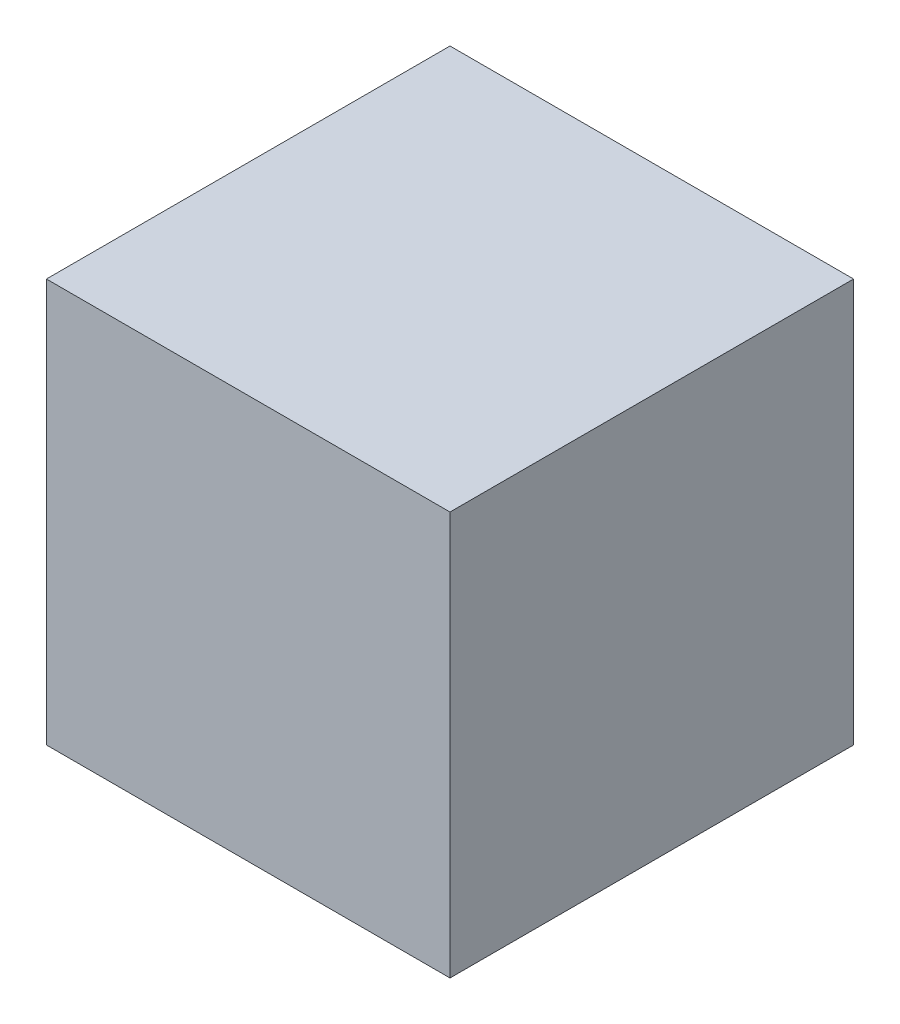
SolidWorks part; units mm, degrees
ref_plane "Front Plane" through (0, 0, 0) normal (0, 0, 1) x (1, 0, 0)
ref_plane "Top Plane" through (0, 0, 0) normal (0, 1, 0) x (1, 0, 0)
ref_plane "Right Plane" through (0, 0, 0) normal (1, 0, 0) x (0, 0, -1)
sketch "Sketch1" plane through (0, 0, 0) normal (0, 0, 1) x (1, 0, 0)
  line L1 (-50, -50) -> (50, -50)
  line L2 (-50, -50) -> (-50, 50)
  line L3 (-50, 50) -> (50, 50)
  line L4 (50, -50) -> (50, 50)
  line L5 (-50, -50) -> (50, 50) construction
  line L6 (-50, 50) -> (50, -50) construction
  point P0 (0, 0)
  dimension "D1" = 100
extrude "Boss-Extrude1" add sketch "Sketch1" along normal blind 100
